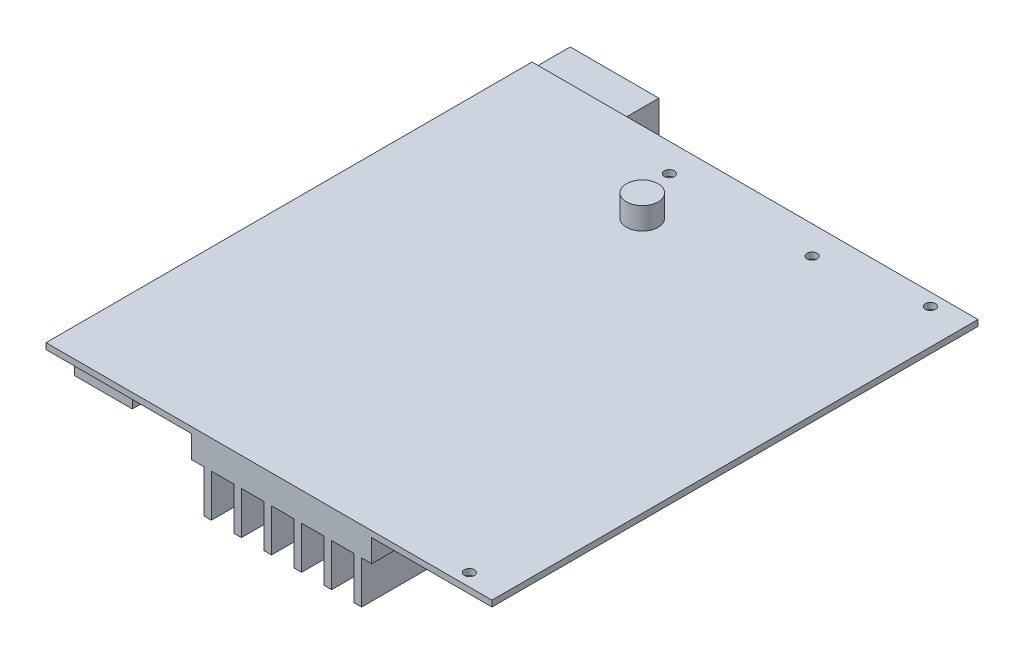
SolidWorks part; units mm, degrees
ref_plane "前视基准面" through (0, 0, 0) normal (0, 0, 1) x (1, 0, 0)
ref_plane "上视基准面" through (0, 0, 0) normal (0, 1, 0) x (1, 0, 0)
ref_plane "右视基准面" through (0, 0, 0) normal (1, 0, 0) x (0, 0, -1)
sketch "草图1" plane through (0, 0, 0) normal (0, 1, 0) x (1, 0, 0)
  line L0 (-7, 94.5) -> (-7, 2.5) construction
  line L5 (-89, 97) -> (0, 97)
  line L6 (-89, 97) -> (-89, 0)
  line L7 (-89, 0) -> (0, 0)
  line L8 (0, 97) -> (0, 0)
  line L9 (-75.4, 69.75) -> (-89, 69.75) construction
  line L10 (-75.4, 69.75) -> (-75.4, 56.65) construction
  line L11 (-75.4, 56.65) -> (-89, 56.65) construction
  line L12 (-89, 69.75) -> (-89, 56.65) construction
  line L13 (-71.3, 105.1) -> (-89, 105.1) construction
  line L14 (-71.3, 105.1) -> (-71.3, 90) construction
  line L15 (-71.3, 90) -> (-89, 90) construction
  line L16 (-89, 105.1) -> (-89, 90) construction
  line L17 (-56, 91.4) -> (-27.5, 91.4) construction
  circle A0 centre (-7, 94.5) radius 1
  circle A1 centre (-7, 2.5) radius 1
  circle A2 centre (-56, 91.4) radius 1
  circle A3 centre (-27.5, 91.4) radius 1
  point P9 (-89, 48.5)
  point P10 (-7, 48.5)
  dimension "D11" = 2
  dimension "D15" = 2
  dimension "D1" = 97
  dimension "D2" = 89
  dimension "D3" = 13.1
  dimension "D4" = 13.6
  dimension "D5" = 17.7
  dimension "D6" = 15.1
  dimension "D7" = 40.35
  dimension "D8" = 8.1
  dimension "D9" = 7
  dimension "D10" = 92
  dimension "D12" = 28.5
  dimension "D13" = 5.6
  dimension "D14" = 33
extrude "凸台-拉伸1" add sketch "草图1" along normal blind 1.2
sketch "草图2" plane through (0, 1.2, 0) normal (0, 1, 0) x (1, 0, 0)
  line L0 (0, 0) -> (0, 97) construction
  line L1 (0, 97) -> (-89, 97) construction
  circle A0 centre (-51, 81) radius 3.15
  dimension "D1" = 6.3
  dimension "D2" = 51
  dimension "D3" = 16
extrude "凸台-拉伸2" add sketch "草图2" along normal blind 4.4
sketch "草图3" plane through (0, 0, 0) normal (0, -1, 0) x (1, 0, 0)
  line L0 (-89, 0) -> (0, 0) construction
  line L1 (-60, 0) -> (-24, 0)
  line L2 (-60, 0) -> (-60, -97)
  line L3 (-60, -97) -> (-24, -97)
  line L4 (-24, 0) -> (-24, -97)
  line L5 (0, -97) -> (-89, -97) construction
  line L6 (0, 0) -> (0, -97) construction
  dimension "D1" = 24
  dimension "D2" = 36
extrude "凸台-拉伸3" add sketch "草图3" along normal blind 4.5
sketch "草图4" plane through (0, 0, -97) normal (0, 0, -1) x (-1, 0, 0)
  line L0 (60, -4.5) -> (24, -4.5) construction
  line L1 (26, -4.5) -> (27.5, -4.5)
  line L2 (26, -4.5) -> (26, -13)
  line L3 (26, -13) -> (27.5, -13)
  line L4 (27.5, -4.5) -> (27.5, -13)
  line L5 (24, -4.5) -> (24, 0) construction
  line L6 (32, -4.5) -> (32, -13)
  line L7 (32, -4.5) -> (33.5, -4.5)
  line L8 (33.5, -4.5) -> (33.5, -13)
  line L9 (32, -13) -> (33.5, -13)
  line L10 (38, -4.5) -> (38, -13)
  line L11 (38, -4.5) -> (39.5, -4.5)
  line L12 (39.5, -4.5) -> (39.5, -13)
  line L13 (38, -13) -> (39.5, -13)
  line L14 (44, -4.5) -> (44, -13)
  line L15 (44, -4.5) -> (45.5, -4.5)
  line L16 (45.5, -4.5) -> (45.5, -13)
  line L17 (44, -13) -> (45.5, -13)
  line L18 (50, -4.5) -> (50, -13)
  line L19 (50, -4.5) -> (51.5, -4.5)
  line L20 (51.5, -4.5) -> (51.5, -13)
  line L21 (50, -13) -> (51.5, -13)
  line L22 (56, -4.5) -> (56, -13)
  line L23 (56, -4.5) -> (57.5, -4.5)
  line L24 (57.5, -4.5) -> (57.5, -13)
  line L25 (56, -13) -> (57.5, -13)
  dimension "D1" = 8.5
  dimension "D2" = 1.5
  dimension "D3" = 2
  dimension "D4" = 6
extrude "凸台-拉伸5" add sketch "草图4" against normal through all
sketch "草图5" plane through (0, 0, 0) normal (0, -1, 0) x (1, 0, 0)
  line L0 (-89, -97) -> (-89, 0) construction
  line L1 (-89, -56.85) -> (-75.4, -56.85)
  line L2 (-89, -56.85) -> (-89, -69.95)
  line L3 (-89, -69.95) -> (-75.4, -69.95)
  line L4 (-75.4, -56.85) -> (-75.4, -69.95)
  line L5 (-60, -97) -> (-89, -97) construction
  dimension "D1" = 13.6
  dimension "D2" = 13.1
  dimension "D5" = 40.15
extrude "凸台-拉伸6" add sketch "草图5" along normal blind 7.3
sketch "草图6" plane through (0, 0, 0) normal (0, -1, 0) x (1, 0, 0)
  line L0 (-89, -97) -> (-89, -69.95) construction
  line L1 (-89, -89.41) -> (-71.3, -89.41)
  line L2 (-89, -89.41) -> (-89, -104.61)
  line L3 (-89, -104.61) -> (-71.3, -104.61)
  line L4 (-71.3, -89.41) -> (-71.3, -104.61)
  line L6 (-60, -97) -> (-89, -97) construction
  dimension "D1" = 17.7
  dimension "D2" = 7.61
  dimension "D3" = 15.2
extrude "凸台-拉伸7" add sketch "草图6" along normal blind 14.8
sketch "草图7" plane through (0, 0, 0) normal (0, -1, 0) x (1, 0, 0)
  line L0 (-89, -56.85) -> (-89, 0) construction
  line L1 (-89, -5.73) -> (-77.5, -5.73)
  line L2 (-89, -5.73) -> (-89, -15.23)
  line L3 (-89, -15.23) -> (-77.5, -15.23)
  line L4 (-77.5, -5.73) -> (-77.5, -15.23)
  line L5 (-60, -97) -> (-71.3, -97) construction
  dimension "D1" = 11.5
  dimension "D2" = 9.5
  dimension "D3" = 91.27
extrude "凸台-拉伸8" add sketch "草图7" along normal blind 7.38
